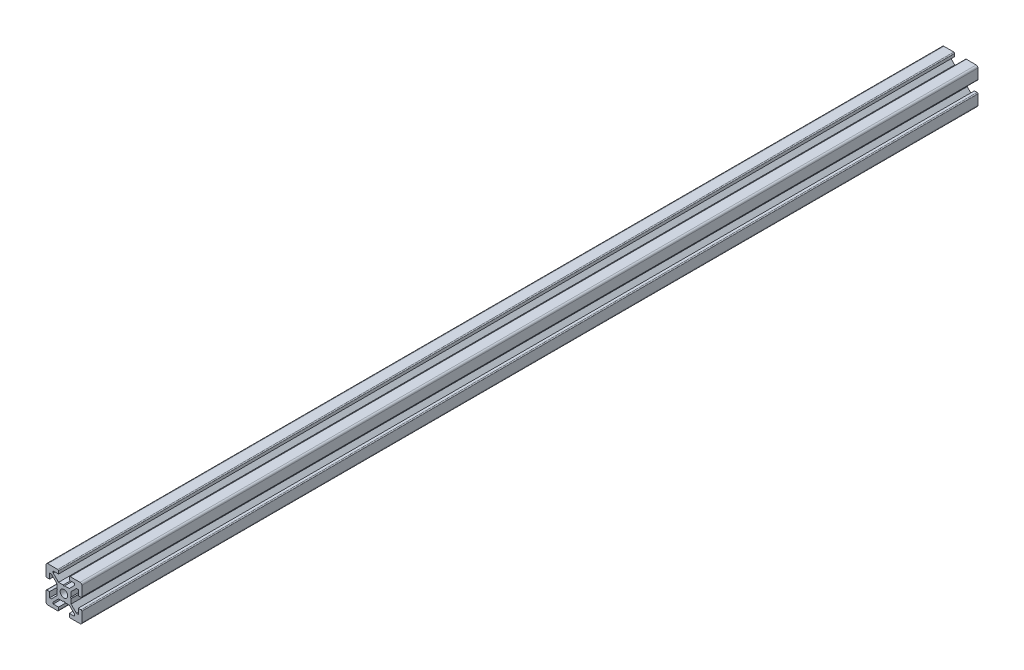
SolidWorks part; units mm, degrees
material "Lega 6061"
ref_plane "Piano frontale" through (0, 0, 0) normal (0, 0, 1) x (1, 0, 0)
ref_plane "Piano superiore" through (0, 0, 0) normal (0, 1, 0) x (1, 0, 0)
ref_plane "Piano destro" through (0, 0, 0) normal (1, 0, 0) x (0, 0, -1)
sketch "Schizzo1" plane through (0, 0, 0) normal (0, 0, 1) x (1, 0, 0)
  line L0 (0, 0) -> (-10, 0) construction
  line L1 (0, 0) -> (0, 10) construction
  line L2 (-3.6, 0) -> (-4, 0.4)
  line L3 (-4, 0.4) -> (-4, 3)
  line L4 (-4, 3) -> (-7, 6)
  line L5 (-7, 6) -> (-8, 6)
  line L6 (-8, 6) -> (-8, 3)
  line L7 (-8, 3) -> (-9.5, 3)
  line L8 (-10, 3.5) -> (-10, 9)
  line L9 (0, 0) -> (-10, 10) construction
  line L10 (0, 3.6) -> (-0.4, 4)
  line L11 (-0.4, 4) -> (-3, 4)
  line L12 (-3, 4) -> (-6, 7)
  line L13 (-6, 7) -> (-6, 8)
  line L14 (-6, 8) -> (-3, 8)
  line L15 (-3, 8) -> (-3, 9.5)
  line L16 (-3.5, 10) -> (-9, 10)
  line L17 (0, 0) -> (-10, -10) construction
  line L18 (-3.5, -10) -> (-9, -10)
  line L19 (-3, -8) -> (-3, -9.5)
  line L20 (-6, -8) -> (-3, -8)
  line L21 (-6, -7) -> (-6, -8)
  line L22 (-3, -4) -> (-6, -7)
  line L23 (-0.4, -4) -> (-3, -4)
  line L24 (0, -3.6) -> (-0.4, -4)
  line L25 (-10, -3.5) -> (-10, -9)
  line L26 (-8, -3) -> (-9.5, -3)
  line L27 (-8, -6) -> (-8, -3)
  line L28 (-7, -6) -> (-8, -6)
  line L29 (-4, -3) -> (-7, -6)
  line L30 (-4, -0.4) -> (-4, -3)
  line L31 (-3.6, 0) -> (-4, -0.4)
  line L32 (0, 0) -> (10, -10) construction
  line L33 (0, 0) -> (10, 10) construction
  line L34 (3.6, 0) -> (4, -0.4)
  line L35 (4, -0.4) -> (4, -3)
  line L36 (4, -3) -> (7, -6)
  line L37 (7, -6) -> (8, -6)
  line L38 (8, -6) -> (8, -3)
  line L39 (8, -3) -> (9.5, -3)
  line L40 (10, -3.5) -> (10, -9)
  line L41 (0, -3.6) -> (0.4, -4)
  line L42 (0.4, -4) -> (3, -4)
  line L43 (3, -4) -> (6, -7)
  line L44 (6, -7) -> (6, -8)
  line L45 (6, -8) -> (3, -8)
  line L46 (3, -8) -> (3, -9.5)
  line L47 (3.5, -10) -> (9, -10)
  line L48 (3.5, 10) -> (9, 10)
  line L49 (3, 8) -> (3, 9.5)
  line L50 (6, 8) -> (3, 8)
  line L51 (6, 7) -> (6, 8)
  line L52 (3, 4) -> (6, 7)
  line L53 (0.4, 4) -> (3, 4)
  line L54 (0, 3.6) -> (0.4, 4)
  line L55 (10, 3.5) -> (10, 9)
  line L56 (8, 3) -> (9.5, 3)
  line L57 (8, 6) -> (8, 3)
  line L58 (7, 6) -> (8, 6)
  line L59 (4, 3) -> (7, 6)
  line L60 (4, 0.4) -> (4, 3)
  line L61 (3.6, 0) -> (4, 0.4)
  arc A0 (-10, 9) -> (-9, 10) centre (-9, 9) cw
  arc A1 (-3, 9.5) -> (-3.5, 10) centre (-3.5, 9.5) ccw
  arc A2 (-9.5, 3) -> (-10, 3.5) centre (-9.5, 3.5) cw
  arc A3 (-9.5, -3) -> (-10, -3.5) centre (-9.5, -3.5) ccw
  arc A4 (-3, -9.5) -> (-3.5, -10) centre (-3.5, -9.5) cw
  arc A5 (-10, -9) -> (-9, -10) centre (-9, -9) ccw
  arc A6 (10, -9) -> (9, -10) centre (9, -9) cw
  arc A7 (3, -9.5) -> (3.5, -10) centre (3.5, -9.5) ccw
  arc A8 (9.5, -3) -> (10, -3.5) centre (9.5, -3.5) cw
  arc A9 (9.5, 3) -> (10, 3.5) centre (9.5, 3.5) ccw
  arc A10 (3, 9.5) -> (3.5, 10) centre (3.5, 9.5) cw
  arc A11 (10, 9) -> (9, 10) centre (9, 9) ccw
  circle A12 centre (0, 0) radius 2.1
  point P24 (-3, 10)
  point P27 (-10, 3)
  point P49 (-10, -3)
  point P50 (-3, -10)
  point P92 (3, -10)
  point P93 (10, -3)
  point P94 (10, 3)
  point P95 (3, 10)
  dimension "D2" = 1
  dimension "D12" = 0.5
  dimension "D13" = 4.2
  dimension "D3" = 8
  dimension "D4" = 0.4
  dimension "D5" = 45
  dimension "D6" = 6
  dimension "D7" = 12
  dimension "D8" = 20
  dimension "D9" = 2
  dimension "D10" = 4
  dimension "D11" = 45
extrude "Estrusione-Estrusione1" add sketch "Schizzo1" along normal blind 500
sketch "Schizzo2" plane through (-4, 0, 0) normal (-1, 0, 0) x (0, 0, 1)
  line L0 (500, 0) -> (0, 0) construction
  line L1 (0, -0.4) -> (0, -3) construction
  line L2 (500, -0.4) -> (500, -3) construction
  circle A0 centre (25, 0) radius 3
  circle A1 centre (475, 0) radius 3
  dimension "D1" = 6
  dimension "D2" = 25
  dimension "D3" = 25
extrude "Taglio-Estrusione1" cut sketch "Schizzo2" against normal through all
